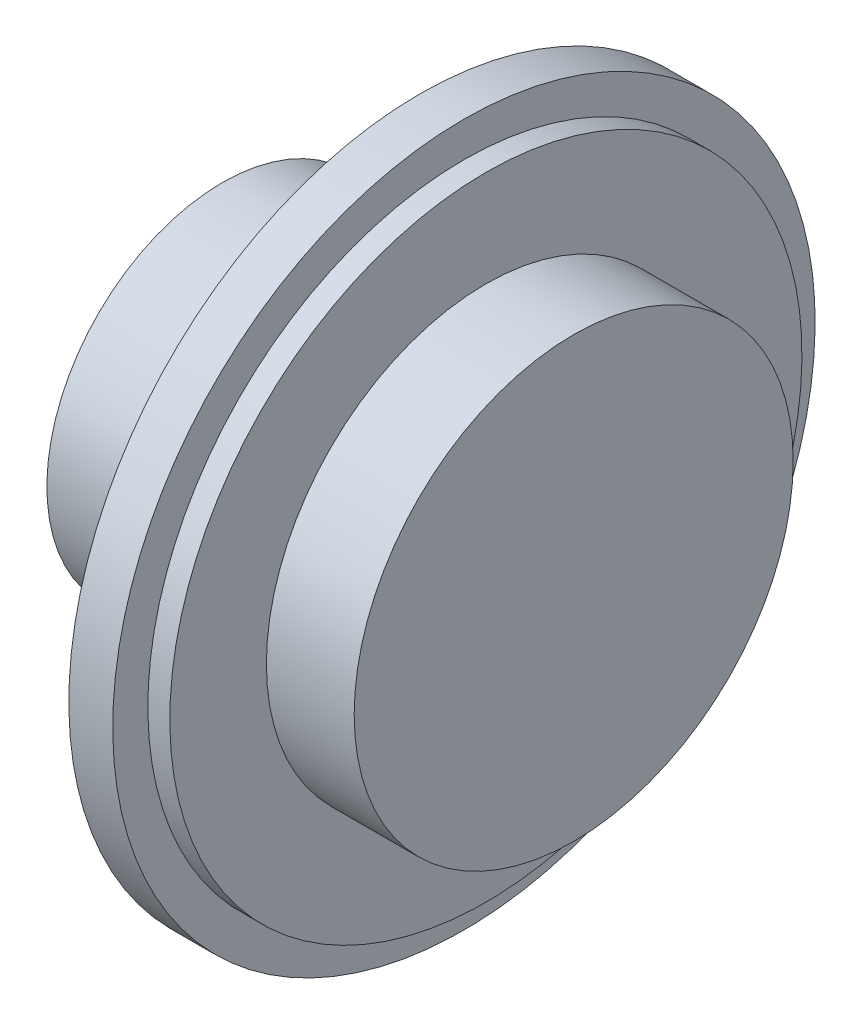
SolidWorks part; units mm, degrees
ref_plane "정면" through (0, 0, 0) normal (0, 0, 1) x (1, 0, 0)
ref_plane "윗면" through (0, 0, 0) normal (0, 1, 0) x (1, 0, 0)
ref_plane "우측면" through (0, 0, 0) normal (1, 0, 0) x (0, 0, -1)
sketch "스케치1" plane through (0, 0, 0) normal (0, 0, 1) x (1, 0, 0)
  line L24 (0, 0) -> (0, 10)
  line L25 (0, 10) -> (10, 10)
  line L26 (10, 10) -> (10, 18)
  line L27 (10, 18) -> (11.25, 18)
  line L28 (11.25, 18) -> (11.25, 20)
  line L29 (11.25, 20) -> (13.75, 20)
  line L30 (13.75, 20) -> (13.75, 18)
  line L31 (13.75, 18) -> (15, 18)
  line L32 (15, 18) -> (15, 12.5)
  line L33 (15, 12.5) -> (20, 12.5)
  line L34 (20, 12.5) -> (20, 0)
  line L35 (20, 0) -> (0, 0)
  point P2 (0, 0)
  point P12 (0, 0)
  point P14 (0, 0)
  point P15 (0, 0)
  point P16 (0, 0)
  point P17 (0, 0)
  dimension "D2" = 10
  dimension "D3" = 5
  dimension "D4" = 12.5
  dimension "D5" = 5
  dimension "D6" = 10
  dimension "D7" = 18
  dimension "D8" = 20
  dimension "D9" = 2.5
  dimension "D10" = 1.25
revolve "회전2" add sketch "스케치1" angle 360 about L35
